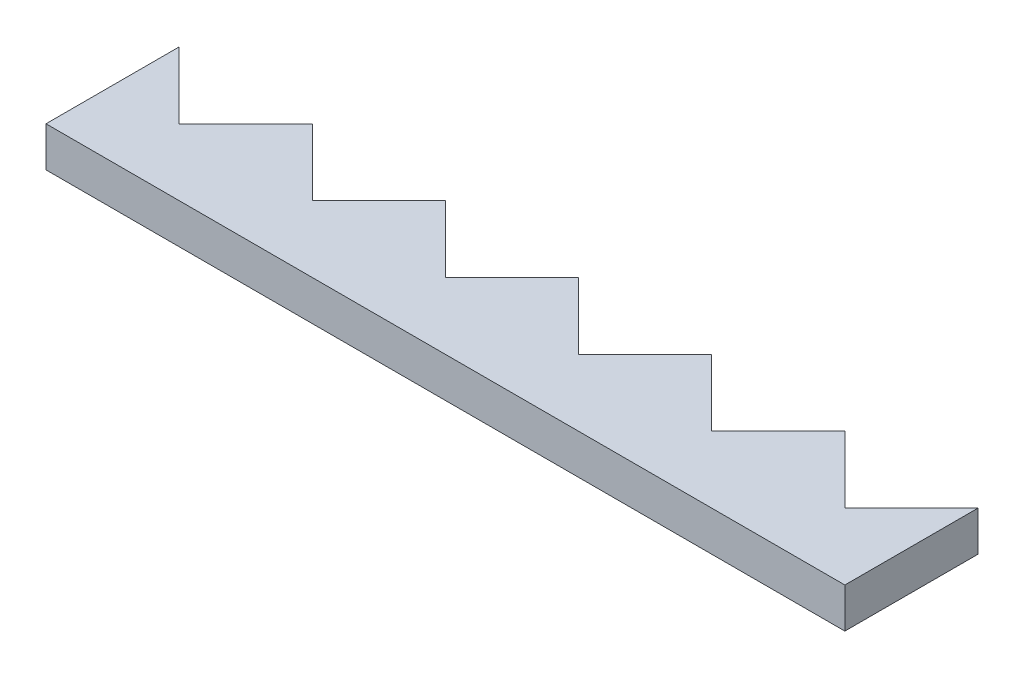
SolidWorks part; units mm, degrees
material "Custom Plastic"
ref_plane "Front Plane" through (0, 0, 0) normal (0, 0, 1) x (1, 0, 0)
ref_plane "Top Plane" through (0, 0, 0) normal (0, 1, 0) x (1, 0, 0)
ref_plane "Right Plane" through (0, 0, 0) normal (1, 0, 0) x (0, 0, -1)
sketch "Sketch1" plane through (0, 0.3303, 0) normal (0, 1, 0) x (1, 0, 0)
  line L0 (0, 0) -> (0, 10)
  line L1 (0, 10) -> (5, 5)
  line L2 (5, 5) -> (10, 10)
  line L3 (50, 10) -> (55, 5)
  line L4 (10, 10) -> (15, 5)
  line L5 (15, 5) -> (20, 10)
  line L6 (20, 10) -> (25, 5)
  line L7 (25, 5) -> (30, 10)
  line L8 (30, 10) -> (35, 5)
  line L9 (35, 5) -> (40, 10)
  line L10 (40, 10) -> (45, 5)
  line L11 (45, 5) -> (50, 10)
  line L16 (0, 0) -> (60, 0)
  line L18 (55, 5) -> (60, 10)
  line L19 (60, 0) -> (60, 10)
  dimension "D1" = 10
  dimension "D2" = 10
  dimension "D3" = 5
  dimension "D4" = 6
extrude "Boss-Extrude1" add sketch "Sketch1" along normal blind 3
